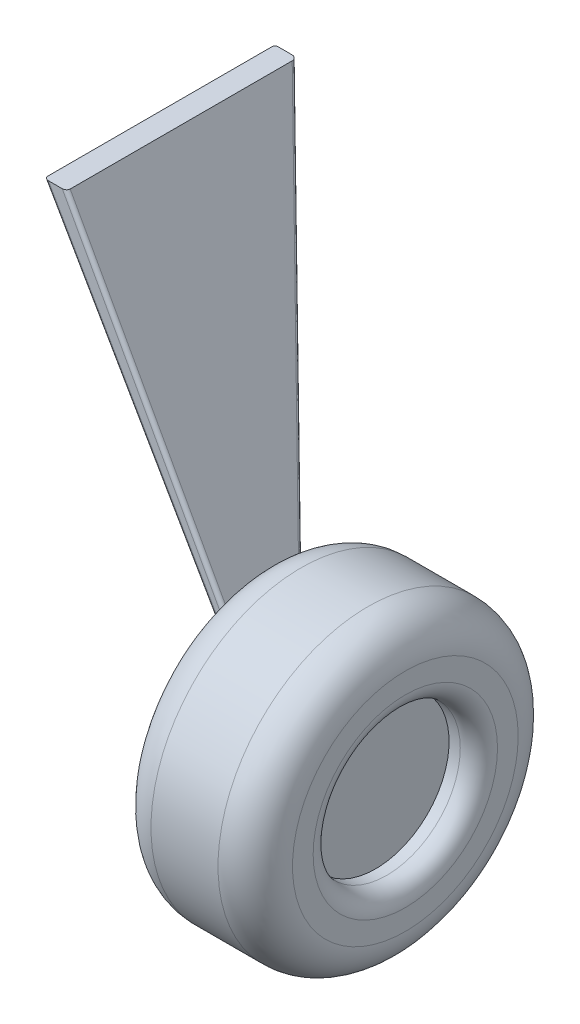
SolidWorks part; units mm, degrees
ref_plane "Front Plane" through (0, 0, 0) normal (0, 0, 1) x (1, 0, 0)
ref_plane "Top Plane" through (0, 0, 0) normal (0, 1, 0) x (1, 0, 0)
ref_plane "Right Plane" through (0, 0, 0) normal (1, 0, 0) x (0, 0, -1)
sketch "Sketch1" plane through (0, 0, 0) normal (1, 0, 0) x (0, 0, -1)
  circle A0 centre (0, 0) radius 201.5
  circle A2 centre (0, 0) radius 98.7681
  dimension "D1" = 403
extrude "Boss-Extrude1" add sketch "Sketch1" along normal blind 190
sketch "Sketch2" plane through (0, 0, 0) normal (-1, 0, 0) x (0, 0, 1)
  circle A1 centre (0, 0) radius 98.7681
extrude "Boss-Extrude2" add sketch "Sketch2" against normal blind 150
fillet "Fillet1" radius 50 2 edges at (190, 0, -201.5) (0, 0, -201.5)
fillet "Fillet2" radius 25 1 edges at (190, 0, -98.7681)
sketch "Sketch4" plane through (0, 0, 0) normal (0, 0, 1) x (1, 0, 0)
  line L0 (0, 0) -> (-265, 481.9492)
  line L1 (-265, 481.9492) -> (-295, 481.9492)
  line L2 (-295, 481.9492) -> (0, -30)
  line L3 (0, 151.5) -> (0, -151.5) construction
  line L4 (0, -30) -> (0, 0)
  dimension "D1" = 30
  dimension "D2" = 30
  dimension "D3" = 550
  dimension "D4" = 265
extrude "Boss-Extrude3" add sketch "Sketch4" against normal blind 310
ref_plane "Plane1" through (-300, 0, 0) normal (-1, 0, 0) x (0, 0, 1)
sketch "Sketch5" plane through (-300, 0, 0) normal (-1, 0, 0) x (0, 0, 1)
  line L0 (-310, 481.9492) -> (-40, -30)
  line L1 (-148.5, -30) -> (0, -30) construction
  line L2 (-310, 481.9492) -> (-310, -30)
  line L3 (-310, -30) -> (-40, -30)
  dimension "D1" = 40
extrude "Cut-Extrude5" cut sketch "Sketch5" against normal blind 300
fillet "Fillet3" radius 5 4 edges at (-147.5, 225.9746, -175) (-132.5, 240.9746, -182.9109) (-132.5, 240.9746, 0) (-147.5, 225.9746, 0)
